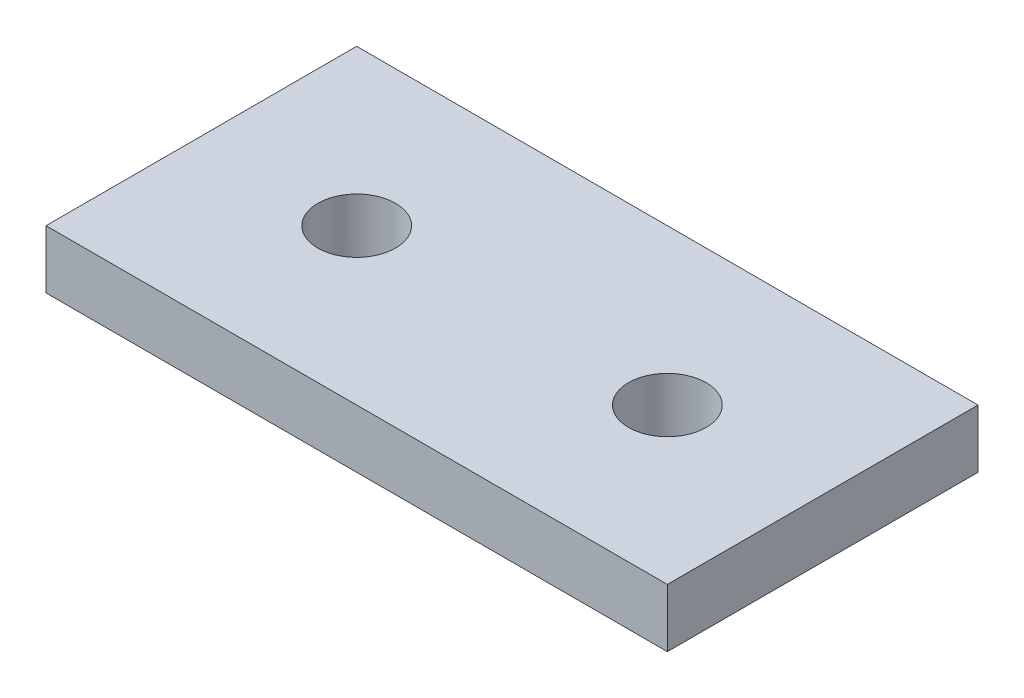
SolidWorks part; units mm, degrees
ref_plane "Front Plane" through (0, 0, 0) normal (0, 0, 1) x (1, 0, 0)
ref_plane "Top Plane" through (0, 0, 0) normal (0, 1, 0) x (1, 0, 0)
ref_plane "Right Plane" through (0, 0, 0) normal (1, 0, 0) x (0, 0, -1)
sketch "Sketch1" plane through (0, 0, 0) normal (0, 1, 0) x (1, 0, 0)
  line L1 (-25.4, -12.7) -> (25.4, -12.7)
  line L2 (-25.4, -12.7) -> (-25.4, 12.7)
  line L3 (-25.4, 12.7) -> (25.4, 12.7)
  line L4 (25.4, -12.7) -> (25.4, 12.7)
  line L5 (-25.4, -12.7) -> (25.4, 12.7) construction
  line L6 (-25.4, 12.7) -> (25.4, -12.7) construction
  point P0 (0, 0)
  dimension "D1" = 50.8
  dimension "D2" = 25.4
extrude "Boss-Extrude1" add sketch "Sketch1" along normal mid plane 4.7625
sketch "Sketch2" plane through (0, 2.3813, 0) normal (0, 1, 0) x (1, 0, 0)
  line L0 (-25.4, 12.7) -> (-25.4, -12.7) construction
  line L1 (25.4, 12.7) -> (-25.4, 12.7) construction
  line L2 (0, 0) -> (0, 50000) construction
  circle A0 centre (-12.7, 0) radius 3.175
  circle A1 centre (12.7, 0) radius 3.175
  dimension "D3" = 6.35
  dimension "D1" = 12.7
  dimension "D2" = 12.7
extrude "Cut-Extrude1" cut sketch "Sketch2" against normal up to next
